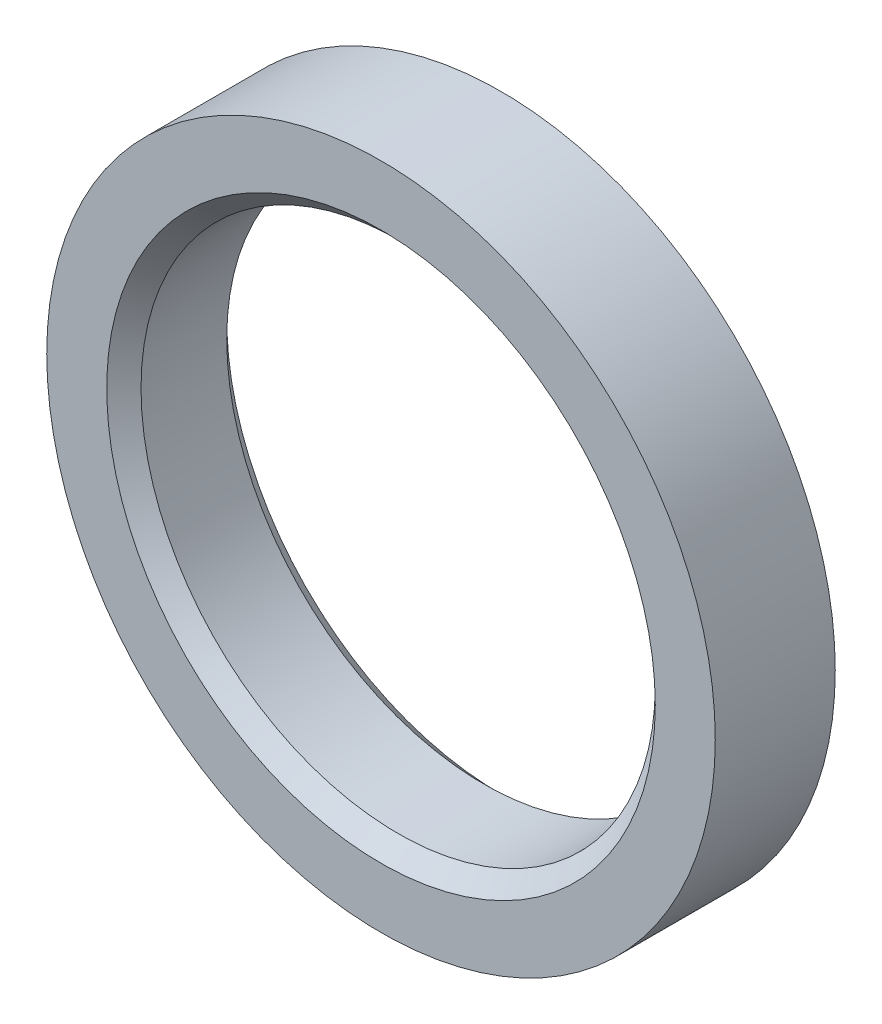
SolidWorks part; units mm, degrees
material "PTFE"
ref_plane "Płaszczyzna przednia" through (0, 0, 0) normal (0, 0, 1) x (1, 0, 0)
ref_plane "Płaszczyzna górna" through (0, 0, 0) normal (0, 1, 0) x (1, 0, 0)
ref_plane "Płaszczyzna prawa" through (0, 0, 0) normal (1, 0, 0) x (0, 0, -1)
ref_plane "Płaszczyzna1"
sketch "Szkic1" plane through (0, 0, 0) normal (0, 0, 1) x (1, 0, 0)
  circle A0 centre (0, 0) radius 19.5
  circle A1 centre (0, 0) radius 15
  dimension "D1" = 39
  dimension "D2" = 30
extrude "Wyciągnięcie proste1" add sketch "Szkic1" along normal blind 7 contours A0 A1
chamfer "Faza2" distance 1 distance2 1 2 edges at (15, 0, 7) (15, 0, 0)
